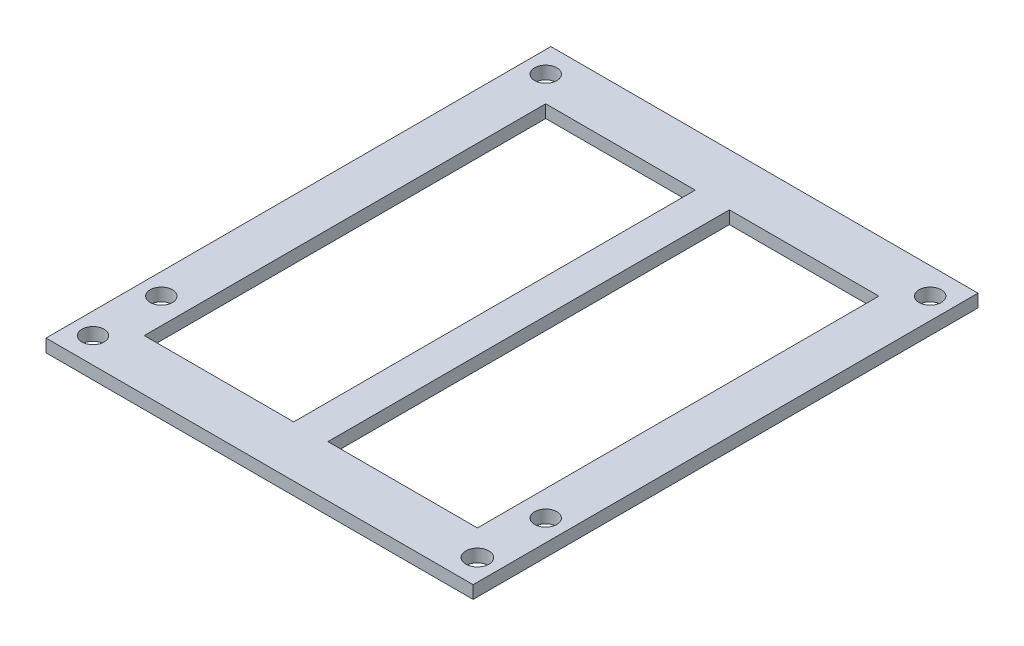
SolidWorks part; units mm, degrees
ref_plane "前视基准面" through (0, 0, 0) normal (0, 0, 1) x (1, 0, 0)
ref_plane "上视基准面" through (0, 0, 0) normal (0, 1, 0) x (1, 0, 0)
ref_plane "右视基准面" through (0, 0, 0) normal (1, 0, 0) x (0, 0, -1)
sketch "草图1" plane through (0, 0, 0) normal (0, 1, 0) x (1, 0, 0)
  line L0 (0, 0) -> (22.5, 0) construction
  line L1 (0, 0) -> (-22.5, 0) construction
  line L2 (2, 50) -> (19.5, 50)
  line L4 (25, 11) -> (25, -3)
  line L5 (25, -3) -> (-25, -3)
  line L6 (-25, -3) -> (-25, 11)
  line L8 (-22.5, 0) -> (-22.5, 8) construction
  line L9 (22.5, 0) -> (22.5, 8) construction
  line L10 (-22.5, 8) -> (-22.5, 53) construction
  line L11 (22.5, 8) -> (22.5, 53) construction
  line L12 (-25, 11) -> (-25, 56.1034)
  line L13 (-25, 56.1034) -> (25, 56.1034)
  line L14 (25, 56.1034) -> (25, 11)
  line L15 (-2, 50) -> (-2, 3)
  line L16 (-2, 50) -> (-19.5, 50)
  line L17 (2, 3) -> (2, 50)
  line L18 (-19.5, 3) -> (-19.5, 50)
  line L19 (-19.5, 3) -> (-2, 3)
  line L20 (2, 3) -> (19.5, 3)
  line L22 (19.5, 3) -> (19.5, 50)
  circle A0 centre (22.5, 0) radius 1.35
  circle A1 centre (-22.5, 0) radius 1.3
  circle A2 centre (-22.5, 8) radius 1.3
  circle A3 centre (22.5, 8) radius 1.3
  circle A4 centre (-22.5, 53) radius 1.3
  circle A5 centre (22.5, 53) radius 1.3
extrude "凸台-拉伸1" add sketch "草图1" along normal blind 1.5
